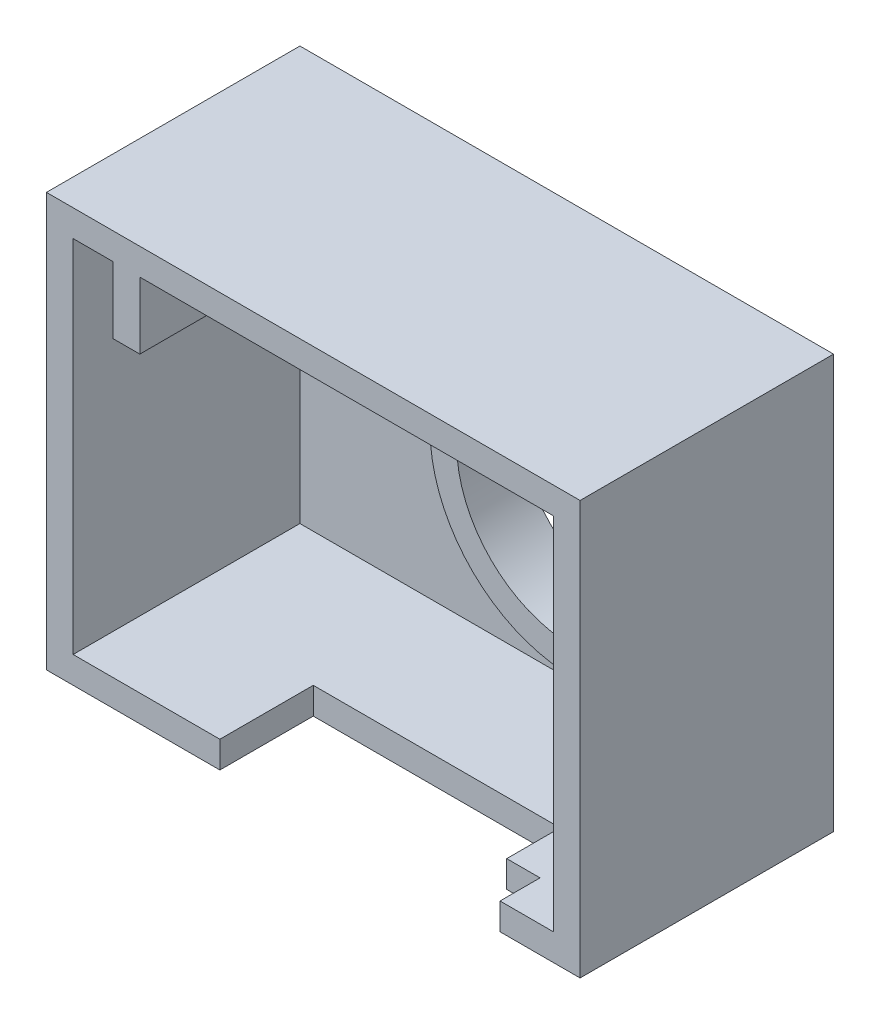
SolidWorks part; units mm, degrees
ref_plane "Front Plane" through (0, 0, 0) normal (0, 0, 1) x (1, 0, 0)
ref_plane "Top Plane" through (0, 0, 0) normal (0, 1, 0) x (1, 0, 0)
ref_plane "Right Plane" through (0, 0, 0) normal (1, 0, 0) x (0, 0, -1)
sketch "Sketch1" plane through (0, 0, 0) normal (0, 0, 1) x (1, 0, 0)
  line L1 (-25, -15.5) -> (15, -15.5)
  line L2 (-25, -15.5) -> (-25, 15.5)
  line L3 (-25, 15.5) -> (15, 15.5)
  line L4 (15, -15.5) -> (15, 15.5)
  circle A0 centre (0, 0) radius 8.75
  point P8 (-25, 0)
  dimension "D1" = 17.5
  dimension "D2" = 40
  dimension "D3" = 31
  dimension "D4" = 25
extrude "Boss-Extrude1" add sketch "Sketch1" against normal blind 19
shell "Shell1" thickness 2
sketch "Sketch2" plane through (0, 0, 0) normal (0, 0, 1) x (1, 0, 0)
  circle A0 centre (0, 0) radius 8.75
  circle A1 centre (0, 0) radius 10.75
  circle A2 centre (0, 0) radius 8.75 construction
  circle A3 centre (0, 0) radius 10.75 construction
extrude "Cut-Extrude1" cut sketch "Sketch2" against normal offset from surface (14.5 mm away) 2.5 up to face at (-10.75, 0, -17)
sketch "Sketch3" plane through (0, 0, -17) normal (0, 0, 1) x (1, 0, 0)
  line L0 (-23, 13.5) -> (-23, -13.5) construction
  line L1 (-20, 13.5) -> (-18, 13.5)
  line L2 (-20, 13.5) -> (-20, 8.5)
  line L3 (-20, 8.5) -> (-18, 8.5)
  line L4 (-18, 13.5) -> (-18, 8.5)
  line L5 (13, 13.5) -> (-23, 13.5) construction
  dimension "D1" = 2
  dimension "D2" = 5
  dimension "D3" = 3
extrude "Boss-Extrude2" add sketch "Sketch3" along normal up to surface (17 mm away) up to face at (-5, 0, 0)
sketch "Sketch8" plane through (0, 0, -17) normal (0, 0, 1) x (1, 0, 0)
  line L0 (13, 13.5) -> (-18, 13.5) construction
  line L1 (-18, 6.5) -> (-11, 6.5)
  line L2 (-18, 6.5) -> (-18, 13.5)
  line L3 (-18, 13.5) -> (-11, 13.5)
  line L4 (-11, 6.5) -> (-11, 13.5)
  line L5 (-18, 8.5) -> (-18, 13.5) construction
  dimension "D1" = 7
  dimension "D2" = 7
extrude "Boss-Extrude3" add sketch "Sketch8" along normal blind 3
hole_wizard "CBORE for M3 SHCS1" positions "Sketch7" profile "Sketch5" counterbore size "M3" standard "ANSI Metric" end condition through all
sketch "Sketch7" plane through (0, 0, -19) normal (0, 0, -1) x (-1, 0, 0)
  line L0 (18, 13.5) -> (18, 8.5) construction
  line L1 (-13, 13.5) -> (18, 13.5) construction
  point P0 (15, 10.5)
  dimension "D1" = 3
  dimension "D2" = 3
sketch "Sketch5" plane through (-15, 10.5, -19) normal (1, 0, 0) x (0, 1, 0)
  line L0 (0, 0) -> (0, 19)
  line L1 (0, 19) -> (1.7, 19)
  line L3 (1.7, 19) -> (1.7, 3)
  line L4 (1.7, 3) -> (3.25, 3)
  line L5 (3.25, 3) -> (3.25, 0)
  line L7 (3.25, 0) -> (0, 0)
  line L11 (0, -6.35) -> (0, 107.95) construction
  dimension "Thru Hole Dia." = 3.4
  dimension "Thru Hole Depth" = 19
  dimension "C'Bore Dia." = 6.5
  dimension "C'Bore Depth" = 3
sketch "Sketch9" plane through (0, -15.5, 0) normal (0, -1, 0) x (1, 0, 0)
  line L0 (-25, 0) -> (15, 0) construction
  line L1 (-12, 0) -> (6.5, 0)
  line L2 (-12, 0) -> (-12, -7)
  line L3 (-12, -7) -> (6.5, -7)
  line L4 (6.5, -3) -> (6.5, -7)
  line L5 (-25, -19) -> (-25, 0) construction
  line L6 (15, -19) -> (15, 0) construction
  line L7 (6.5, -3) -> (9, -3)
  line L8 (9, -3) -> (9, 0)
  line L9 (-25, 0) -> (15, 0) construction
  line L10 (9, 0) -> (6.5, 0)
  dimension "D1" = 18.5
  dimension "D2" = 13
  dimension "D3" = 7
  dimension "D5" = 6
  dimension "D6" = 3
  dimension "D7" = 2.5
extrude "Cut-Extrude3" cut sketch "Sketch9" against normal up to next
